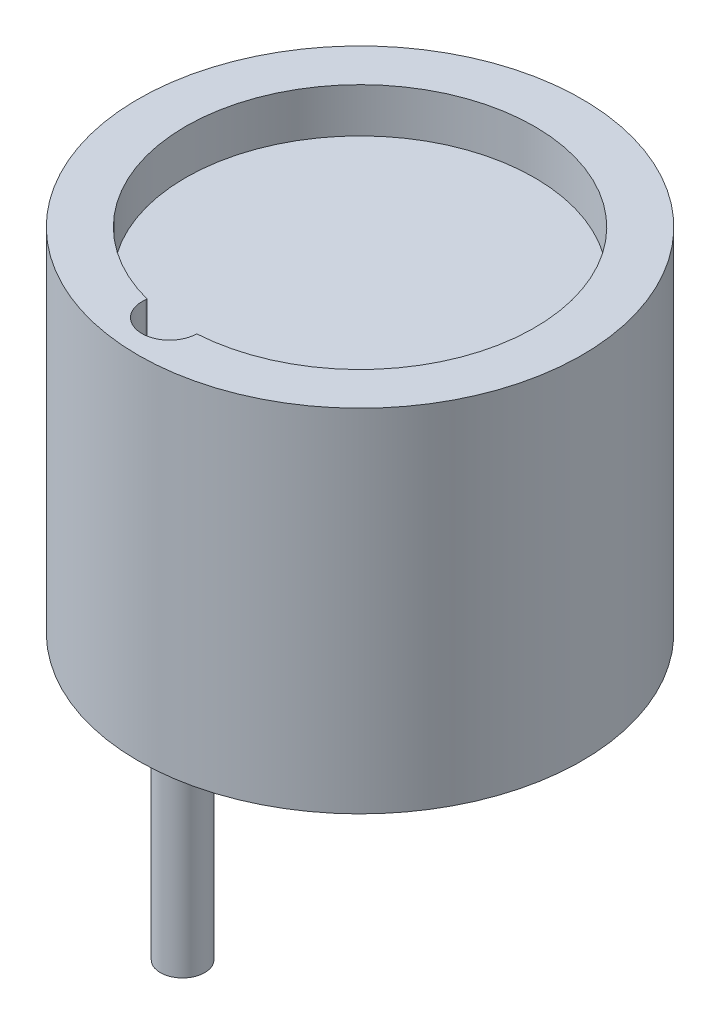
SolidWorks part; units mm, degrees
ref_plane "Front Plane" through (0, 0, 0) normal (0, 0, 1) x (1, 0, 0)
ref_plane "Top Plane" through (0, 0, 0) normal (0, 1, 0) x (1, 0, 0)
ref_plane "Right Plane" through (0, 0, 0) normal (1, 0, 0) x (0, 0, -1)
sketch "Sketch1" plane through (0, 0, 0) normal (0, 1, 0) x (1, 0, 0)
  circle A0 centre (0, 0) radius 6
extrude "Boss-Extrude1" add sketch "Sketch1" against normal blind 9.5
sketch "Sketch2" plane through (0, 0, 0) normal (0, 1, 0) x (1, 0, 0)
  line L1 (0.2966, -4.7084) -> (0.2851, -4.7947)
  line L2 (-1.1926, -4.5645) -> (-1.1968, -4.5966)
  arc A0 (0.2966, -4.7084) -> (-1.1926, -4.5645) centre (0, 0) ccw
  arc A2 (-1.1968, -4.5966) -> (0.2851, -4.7947) centre (-0.4559, -4.6956) ccw
  point P5 (-0.3043, -3.5615)
extrude "Cut-Extrude1" cut sketch "Sketch2" against normal blind 1.2
sketch "Sketch3" plane through (0, -9.5, 0) normal (0, -1, 0) x (1, 0, 0)
  circle A0 centre (-0.7387, 4.0606) radius 0.6
  point P2 (0, 4.1219)
extrude "Boss-Extrude3" add sketch "Sketch3" along normal blind 6 separate body contours A0
sketch "Sketch4" plane through (0, -9.5, 0) normal (0, -1, 0) x (1, 0, 0)
  circle A0 centre (0.4427, -4.5952) radius 0.6
extrude "Boss-Extrude4" add sketch "Sketch4" along normal blind 4 separate body
